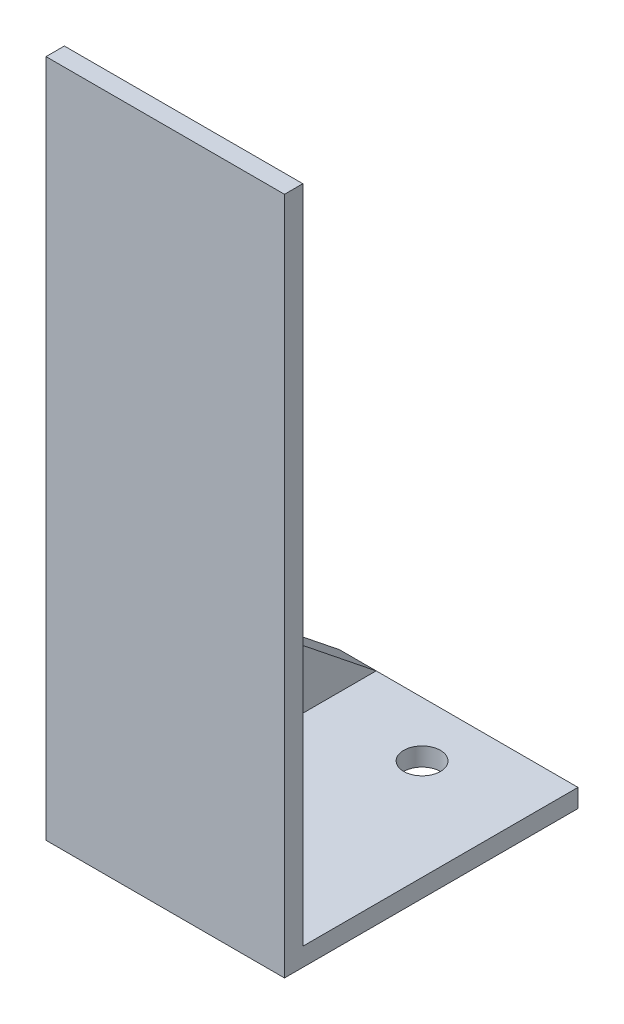
SolidWorks part; units mm, degrees
ref_plane "Front Plane" through (0, 0, 0) normal (0, 0, 1) x (1, 0, 0)
ref_plane "Top Plane" through (0, 0, 0) normal (0, 1, 0) x (1, 0, 0)
ref_plane "Right Plane" through (0, 0, 0) normal (1, 0, 0) x (0, 0, -1)
sketch "Sketch1" plane through (0, 0, 0) normal (1, 0, 0) x (0, 0, -1)
  line L5 (0, 0) -> (-101.6, 0)
  line L6 (0, 0) -> (0, 6.35)
  line L11 (0, 6.35) -> (-95.25, 6.35)
  line L12 (-101.6, 0) -> (-101.6, 6.35)
  line L14 (-101.6, 6.35) -> (-101.6, 234.95)
  line L15 (-101.6, 234.95) -> (-95.25, 234.95)
  line L16 (-95.25, 6.35) -> (-95.25, 234.95)
  dimension "D1" = 101.6
  dimension "D2" = 6.35
  dimension "D3" = 234.95
  dimension "D4" = 6.35
  dimension "D5" = 6.35
extrude "Boss-Extrude1" add sketch "Sketch1" along normal blind 146.05
sketch "Sketch2" plane through (0, 0, 101.6) normal (0, 0, 1) x (1, 0, 0)
  line L1 (0, 0) -> (63.5, 0)
  line L2 (0, 0) -> (0, 234.95)
  line L3 (0, 234.95) -> (63.5, 234.95)
  line L4 (63.5, 0) -> (63.5, 234.95)
  dimension "D1" = 234.95
  dimension "D2" = 63.5
extrude "Cut-Extrude1" cut sketch "Sketch2" against normal blind 146.05
sketch "Sketch3" plane through (63.5, 0, 0) normal (-1, 0, 0) x (0, 0, 1)
  line L5 (0, 6.35) -> (95.25, 82.55)
  line L6 (95.25, 6.35) -> (95.25, 234.95) construction
  line L7 (95.25, 82.55) -> (95.25, 6.35)
  line L8 (95.25, 6.35) -> (0, 6.35)
  dimension "D1" = 76.2
extrude "Boss-Extrude2" add sketch "Sketch3" against normal blind 12.7
sketch "Sketch4" plane through (0, 6.35, 0) normal (0, 1, 0) x (1, 0, 0)
  circle A0 centre (111.125, -19.05) radius 6.35
  circle A1 centre (111.125, -82.55) radius 6.35
  dimension "D1" = 12.7
  dimension "D2" = 12.7
  dimension "D3" = 34.925
  dimension "D4" = 19.05
  dimension "D5" = 19.05
extrude "Cut-Extrude2" cut sketch "Sketch4" against normal blind 12.7
